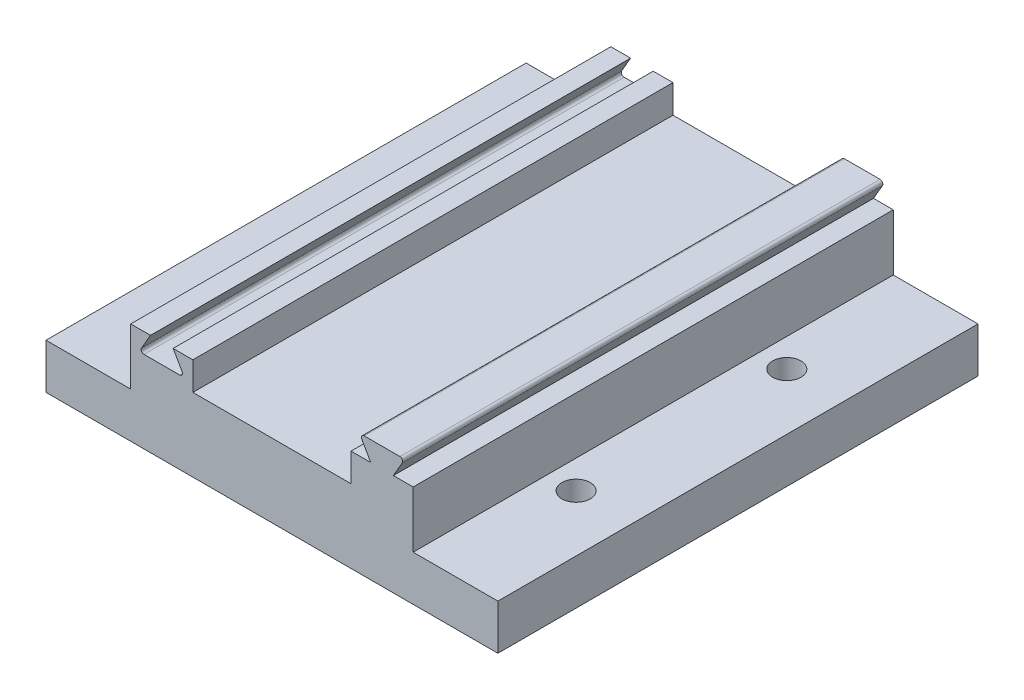
SolidWorks part; units mm, degrees
ref_plane "Front Plane" through (0, 0, 0) normal (0, 0, 1) x (1, 0, 0)
ref_plane "Top Plane" through (0, 0, 0) normal (0, 1, 0) x (1, 0, 0)
ref_plane "Right Plane" through (0, 0, 0) normal (1, 0, 0) x (0, 0, -1)
sketch "Sketch7" plane through (0, 0, 0) normal (0, 1, 0) x (1, 0, 0)
  line L1 (-25, -42.5) -> (25, -42.5)
  line L2 (-25, -42.5) -> (-25, 42.5)
  line L3 (-25, 42.5) -> (25, 42.5)
  line L4 (25, -42.5) -> (25, 42.5)
  line L5 (-25, -42.5) -> (25, 42.5) construction
  line L6 (-25, 42.5) -> (25, -42.5) construction
  point P0 (0, 0)
  dimension "D1" = 50
  dimension "D2" = 85
extrude "Boss-Extrude5" add sketch "Sketch7" along normal blind 10 contours L3 L4 L1 L2
sketch "Sketch8" plane through (0, 10, 0) normal (0, 1, 0) x (1, 0, 0)
  line L0 (-14, 42.5) -> (-14, -42.5)
  line L1 (14, 42.5) -> (14, -42.5)
  line L2 (0, 0) -> (14, 0) construction
  line L3 (0, 0) -> (-14, 0) construction
  line L4 (-25, 42.5) -> (-25, -42.5)
  line L5 (-25, -42.5) -> (25, -42.5)
  line L6 (25, -42.5) -> (25, 42.5)
  line L7 (25, 42.5) -> (-25, 42.5)
  line L8 (-25, 42.5) -> (-25, -42.5)
  line L9 (-25, -42.5) -> (25, -42.5)
  line L10 (25, -42.5) -> (25, 42.5)
  line L11 (25, 42.5) -> (-25, 42.5)
  line M8 (-25, -42.5) -> (25, -42.5)
  line M10 (25, 42.5) -> (-25, 42.5)
  dimension "D2" = 28
  dimension "D1" = 0
extrude "Cut-Extrude1" cut sketch "Sketch8" against normal blind 5 contours L1 L0 M10 M8
sketch "Sketch10" plane through (0, 0, 42.5) normal (0, 0, 1) x (1, 0, 0)
  line L0 (-19.5, 10) -> (-19.5, -3.3178) construction
  line L1 (17, 11.9016) -> (17, -2.979) construction
  line L8 (14, 10) -> (14, 5)
  line L9 (14, 5) -> (-14, 5)
  line L10 (-14, 5) -> (-14, 10)
  line L11 (-14, 10) -> (-25, 10)
  line L12 (-25, 10) -> (-25, 0)
  line L13 (-25, 0) -> (25, 0)
  line L14 (25, 0) -> (25, 10)
  line L15 (25, 10) -> (14, 10)
  line L16 (14, 10) -> (14, 5)
  line L17 (14, 5) -> (-14, 5)
  line L18 (-14, 5) -> (-14, 10)
  line L19 (-14, 10) -> (-25, 10)
  line L20 (-25, 10) -> (-25, 0)
  line L21 (-25, 0) -> (25, 0)
  line L22 (25, 0) -> (25, 10)
  line L23 (25, 10) -> (14, 10)
  dimension "D1" = 0
sketch "Sketch11" plane through (0, 10, 0) normal (0, 1, 0) x (1, 0, 0)
  line L4 (14, 42.5) -> (14, -42.5)
  line L5 (14, -42.5) -> (25, -42.5)
  line L7 (25, 42.5) -> (14, 42.5)
  line L9 (14, -42.5) -> (25, -42.5)
  line L11 (25, 42.5) -> (14, 42.5)
  line L12 (14, 42.5) -> (14, -42.5)
  line L14 (25, -42.5) -> (25, 42.5)
  line L15 (25, -42.5) -> (25, 42.5)
  dimension "D1" = 0
extrude "Boss-Extrude6" add sketch "Sketch11" along normal blind 3.5
sketch "Sketch12" plane through (0, 0, 42.5) normal (0, 0, 1) x (1, 0, 0)
  line L8 (14, 10) -> (14, 5)
  line L9 (14, 5) -> (-14, 5)
  line L10 (-14, 5) -> (-14, 10)
  line L11 (-14, 10) -> (-25, 10)
  line L12 (-25, 10) -> (-25, 0)
  line L13 (-25, 0) -> (25, 0)
  line L14 (25, 0) -> (25, 10)
  line L15 (25, 10) -> (14, 10)
  line L16 (14, 10) -> (14, 5)
  line L17 (14, 5) -> (-14, 5)
  line L18 (-14, 5) -> (-14, 10)
  line L19 (-14, 10) -> (-25, 10)
  line L20 (-25, 10) -> (-25, 0)
  line L21 (-25, 0) -> (25, 0)
  line L22 (25, 0) -> (25, 10)
  line L23 (25, 10) -> (14, 10)
  line L33 (-21.5, 10) -> (-17.5, 10)
  line L34 (-17.5, 10) -> (-15.9123, 7.25)
  line L35 (-16.3453, 6.5) -> (-22.6547, 6.5)
  line L36 (-23.0877, 7.25) -> (-21.5, 10)
  line L41 (15.4793, 13.5) -> (17.5, 10)
  line L42 (21.5, 10) -> (23.5207, 13.5)
  line L43 (17.5, 10) -> (21.5, 10)
  line L44 (15.4793, 13.5) -> (23.5207, 13.5)
  line L45 (14, 13.5) -> (14, 5)
  line L46 (14, 5) -> (-14, 5)
  line L47 (-14, 5) -> (-14, 10)
  line L48 (-14, 10) -> (-25, 10)
  line L49 (-25, 10) -> (-25, 0)
  line L50 (-25, 0) -> (25, 0)
  line L51 (25, 0) -> (25, 13.5)
  line L52 (25, 13.5) -> (14, 13.5)
  line L53 (14, 13.5) -> (14, 5)
  line L54 (14, 5) -> (-14, 5)
  line L55 (-14, 5) -> (-14, 10)
  line L56 (-14, 10) -> (-25, 10)
  line L57 (-25, 10) -> (-25, 0)
  line L58 (-25, 0) -> (25, 0)
  line L59 (25, 0) -> (25, 13.5)
  line L60 (25, 13.5) -> (14, 13.5)
  line L61 (14, 10) -> (17.5, 10)
  line L62 (21.5, 10) -> (25, 10)
  arc A6 (-22.6547, 6.5) -> (-23.0877, 7.25) centre (-22.6547, 7) cw
  arc A7 (-15.9123, 7.25) -> (-16.3453, 6.5) centre (-16.3453, 7) cw
  point P8 (-19.5, 10)
  point P15 (19.5, 10)
  point P17 (19.5, 10)
  point P19 (6.7269, 19.2425)
  dimension "D5" = 4
  dimension "D7" = 0.5
  dimension "D3" = 60
  dimension "D4" = 3.5
  dimension "D2" = 60
  dimension "D1" = 0
  dimension "D6" = 0
extrude "Cut-Extrude5" cut sketch "Sketch12" against normal through all contours L36 L33 L34 A7 L35 A6
sketch "Sketch13" plane through (0, 0, 42.5) normal (0, 0, 1) x (1, 0, 0)
  line L0 (25, 10) -> (14, 10) construction
  line L1 (25, 10) -> (14, 10)
  line L4 (22.6547, 13.5) -> (16.3453, 13.5)
  line L6 (15.9123, 12.75) -> (17.5, 10)
  line L7 (21.5, 10) -> (23.0877, 12.75)
  line L8 (17.5, 10) -> (21.5, 10)
  line L12 (-23.0877, 7.25) -> (-21.5, 10)
  line L13 (-21.5, 10) -> (-25, 10)
  line L14 (-25, 10) -> (-25, 0)
  line L15 (-25, 0) -> (25, 0)
  line L16 (25, 0) -> (25, 13.5)
  line L17 (25, 13.5) -> (14, 13.5)
  line L18 (14, 13.5) -> (14, 5)
  line L19 (14, 5) -> (-14, 5)
  line L20 (-14, 5) -> (-14, 10)
  line L21 (-14, 10) -> (-17.5, 10)
  line L22 (-17.5, 10) -> (-15.9123, 7.25)
  line L23 (-16.3453, 6.5) -> (-22.6547, 6.5)
  line L24 (-23.0877, 7.25) -> (-21.5, 10)
  line L25 (-21.5, 10) -> (-25, 10)
  line L26 (-25, 10) -> (-25, 0)
  line L27 (-25, 0) -> (25, 0)
  line L28 (25, 0) -> (25, 13.5)
  line L29 (25, 13.5) -> (14, 13.5)
  line L30 (14, 13.5) -> (14, 5)
  line L31 (14, 5) -> (-14, 5)
  line L32 (-14, 5) -> (-14, 10)
  line L33 (-14, 10) -> (-17.5, 10)
  line L34 (-17.5, 10) -> (-15.9123, 7.25)
  line L35 (-16.3453, 6.5) -> (-22.6547, 6.5)
  arc A0 (16.3453, 13.5) -> (15.9123, 12.75) centre (16.3453, 13) ccw
  arc A1 (23.0877, 12.75) -> (22.6547, 13.5) centre (22.6547, 13) ccw
  arc A4 (-16.3453, 6.5) -> (-15.9123, 7.25) centre (-16.3453, 7) ccw
  arc A5 (-16.3453, 6.5) -> (-15.9123, 7.25) centre (-16.3453, 7) ccw
  arc A6 (-23.0877, 7.25) -> (-22.6547, 6.5) centre (-22.6547, 7) ccw
  arc A7 (-23.0877, 7.25) -> (-22.6547, 6.5) centre (-22.6547, 7) ccw
  point P8 (19.5, 10)
  point P10 (19.5, 10)
  line M24 (25, 0) -> (25, 13.5)
  line M25 (25, 13.5) -> (14, 13.5)
  line M26 (14, 13.5) -> (14, 5)
  dimension "D2" = 0.5
  dimension "D3" = 0.5
  dimension "D1" = 0
extrude "Cut-Extrude6" cut sketch "Sketch13" against normal through all contours L6 L1 M25 M26 | L7 L1 M24 M25
sketch "Sketch14" plane through (0, 0, 0) normal (0, -1, 0) x (1, 0, 0)
  line L1 (-40, -42.5) -> (40, -42.5)
  line L2 (-40, -42.5) -> (-40, 42.5)
  line L3 (-40, 42.5) -> (40, 42.5)
  line L4 (-25, 42.5) -> (-25, -42.5)
  line L5 (-25, -42.5) -> (25, -42.5)
  line L6 (25, -42.5) -> (25, 42.5)
  line L7 (25, 42.5) -> (-25, 42.5)
  line L8 (-25, 42.5) -> (-25, -42.5)
  line L9 (-25, -42.5) -> (25, -42.5)
  line L10 (25, -42.5) -> (25, 42.5)
  line L11 (25, 42.5) -> (-25, 42.5)
  line L12 (40, -42.5) -> (40, 42.5)
  line L13 (-40, -42.5) -> (40, 42.5) construction
  line L14 (-40, 42.5) -> (40, -42.5) construction
  point P2 (0, 0)
  line M5 (-25, 42.5) -> (-25, -42.5)
  line M6 (-25, -42.5) -> (25, -42.5)
  line M7 (25, -42.5) -> (25, 42.5)
  line M8 (25, 42.5) -> (-25, 42.5)
  dimension "D2" = 80
  dimension "D1" = 0
extrude "Boss-Extrude7" add sketch "Sketch14" along normal blind 8 contours M8 M5 M6 M7 | L1 L12 L3 M7 | L3 L2 L1 M5
sketch "Sketch18" plane through (0, -8, 0) normal (0, -1, 0) x (1, 0, 0)
  line L1 (30.5, -23.25) -> (-30.5, -23.25)
  line L2 (34.6, -19.15) -> (34.6, 19.15)
  line L3 (30.5, 23.25) -> (-30.5, 23.25)
  line L4 (-34.6, -19.15) -> (-34.6, 19.15)
  line L5 (34.6, -23.25) -> (-34.6, 23.25) construction
  line L6 (34.6, 23.25) -> (-34.6, -23.25) construction
  arc A0 (34.6, 19.15) -> (30.5, 23.25) centre (30.5, 19.15) ccw
  arc A1 (30.5, -23.25) -> (34.6, -19.15) centre (30.5, -19.15) ccw
  arc A2 (-30.5, -23.25) -> (-34.6, -19.15) centre (-30.5, -19.15) cw
  arc A3 (-30.5, 23.25) -> (-34.6, 19.15) centre (-30.5, 19.15) ccw
  point P0 (0, 0)
  dimension "D3" = 4.1
  dimension "D1" = 69.2
  dimension "D2" = 46.5
extrude "Cut-Extrude11" cut sketch "Sketch18" against normal blind 2
sketch "Sketch19" plane through (0, -6, 0) normal (0, -1, 0) x (1, 0, 0)
  line L2 (0, 9.9661) -> (0, -9.2698) construction
  line L3 (-13.5783, 0) -> (16.8858, 0) construction
  line L9 (-34.1, -22.75) -> (34.1, 22.75) construction
  line L10 (-34.1, 22.75) -> (34.1, -22.75) construction
  circle A0 centre (-30, 18.65) radius 2.5106
  circle A4 centre (-30, -18.65) radius 2.5106
  circle A5 centre (30, -18.65) radius 2.5106
  circle A6 centre (30, 18.65) radius 2.5106
  point P17 (0, 0)
  dimension "D3" = 68.2
  dimension "D4" = 45.5
extrude "Cut-Extrude12" cut sketch "Sketch19" against normal through all
equation "\"thigh_width\"= 3cm"
equation "\"thigh_thickeness\"= 1cm"
equation "\"shin_thickness\"= 0.6cm"
equation "\"shin_width\"= 5cm"
equation "\"D1@Sketch7\"=\"thigh_width\"+2cm"
equation "\"link_length\"= 8.5cm"
equation "\"D2@Sketch7\"=\"link_length\""
equation "\"D1@Boss-Extrude5\"=\"thigh_thickeness\""
equation "\"D2@Sketch8\"=\"thigh_width\"-2mm"
equation "\"bolt head\"= 4.2mm'With clearance"
